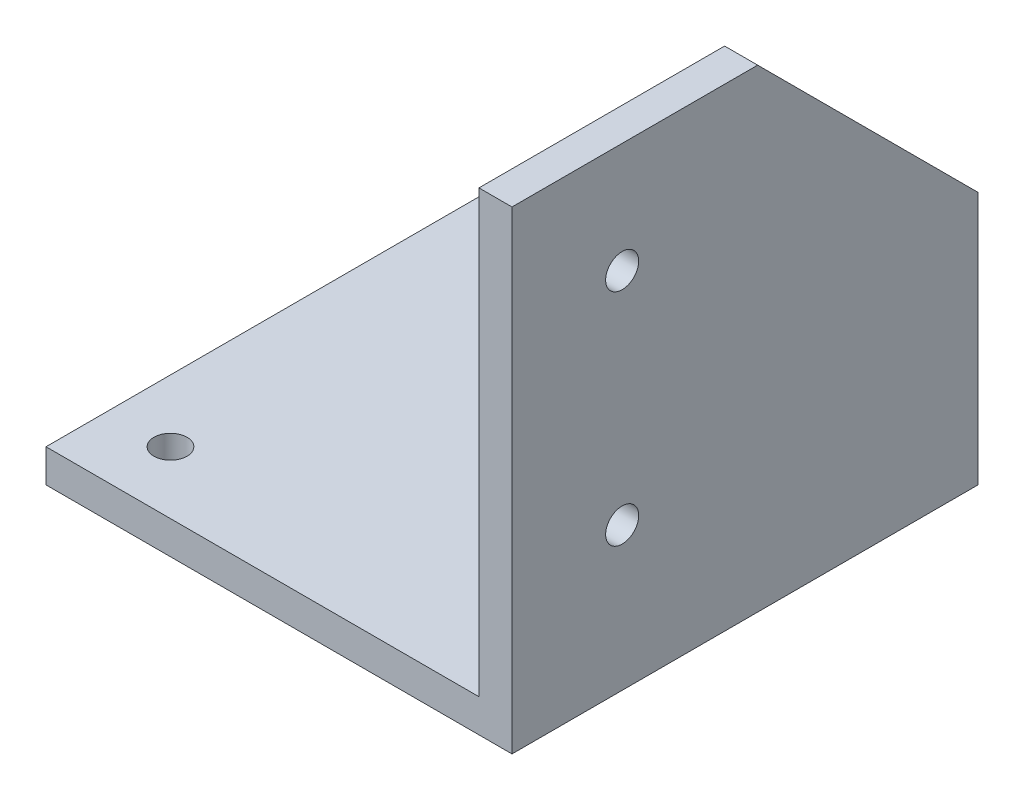
SolidWorks part; units mm, degrees
ref_plane "Front Plane" through (0, 0, 0) normal (0, 0, 1) x (1, 0, 0)
ref_plane "Top Plane" through (0, 0, 0) normal (0, 1, 0) x (1, 0, 0)
ref_plane "Right Plane" through (0, 0, 0) normal (1, 0, 0) x (0, 0, -1)
sketch "Sketch1" plane through (0, 0, 0) normal (0, 1, 0) x (1, 0, 0)
  line L1 (0, 0) -> (42.3, 0)
  line L2 (0, 0) -> (0, 42.3)
  line L3 (0, 42.3) -> (42.3, 42.3)
  line L4 (42.3, 0) -> (42.3, 42.3)
  dimension "D1" = 42.3
  dimension "D2" = 42.3
extrude "Boss-Extrude1" add sketch "Sketch1" along normal blind 3
sketch "Sketch2" plane through (0, 3, 0) normal (0, 1, 0) x (1, 0, 0)
  line L0 (42.3, 0) -> (42.3, 42.3) construction
  line L1 (0, 42.3) -> (0, 0) construction
  line L4 (0, 0) -> (42.3, 0) construction
  line L5 (42.3, 42.3) -> (0, 42.3) construction
  circle A0 centre (5.65, 5.65) radius 1.5
  circle A1 centre (36.65, 5.65) radius 1.5
  circle A2 centre (36.65, 36.65) radius 1.5
  circle A3 centre (5.65, 36.65) radius 1.5
  dimension "D9" = 3
  dimension "D10" = 3
  dimension "D11" = 3
  dimension "D12" = 3
  dimension "D2" = 31
  dimension "D3" = 5.65
  dimension "D4" = 31
  dimension "D5" = 5.65
  dimension "D6" = 31
  dimension "D7" = 5.65
  dimension "D8" = 31
  dimension "D13" = 5.65
extrude "Cut-Extrude1" cut sketch "Sketch2" against normal through all
sketch "Sketch5" plane through (0, 3, 0) normal (0, 1, 0) x (1, 0, 0)
  line L0 (0, 0) -> (42.3, 0) construction
  line L1 (42.3, 42.3) -> (39.3, 42.3)
  line L2 (42.3, 42.3) -> (42.3, 0)
  line L3 (42.3, 0) -> (39.3, 0)
  line L4 (39.3, 42.3) -> (39.3, 0)
  dimension "D1" = 3
extrude "Boss-Extrude2" add sketch "Sketch5" along normal blind 40
sketch "Sketch6" plane through (39.3, 0, 0) normal (-1, 0, 0) x (0, 0, 1)
  line L0 (-42.3, 43) -> (-22.3, 43)
  line L1 (-42.3, 43) -> (0, 43) construction
  line L5 (-42.3, 43) -> (-42.3, 23)
  line L6 (-42.3, 43) -> (-42.3, 3) construction
  line L7 (-42.3, 23) -> (-22.3, 43)
  dimension "D1" = 20
  dimension "D2" = 20
extrude "Cut-Extrude2" cut sketch "Sketch6" against normal blind 40
sketch "Sketch7" plane through (39.3, 0, 0) normal (-1, 0, 0) x (0, 0, 1)
  line L2 (0, 43) -> (0, 3) construction
  line L3 (-22.3, 43) -> (0, 43) construction
  circle A0 centre (-10, 33) radius 1.5
  circle A1 centre (-10, 13) radius 1.5
  dimension "D1" = 3
  dimension "D2" = 3
  dimension "D3" = 10
  dimension "D4" = 10
  dimension "D6" = 20
extrude "Cut-Extrude3" cut sketch "Sketch7" against normal through all
